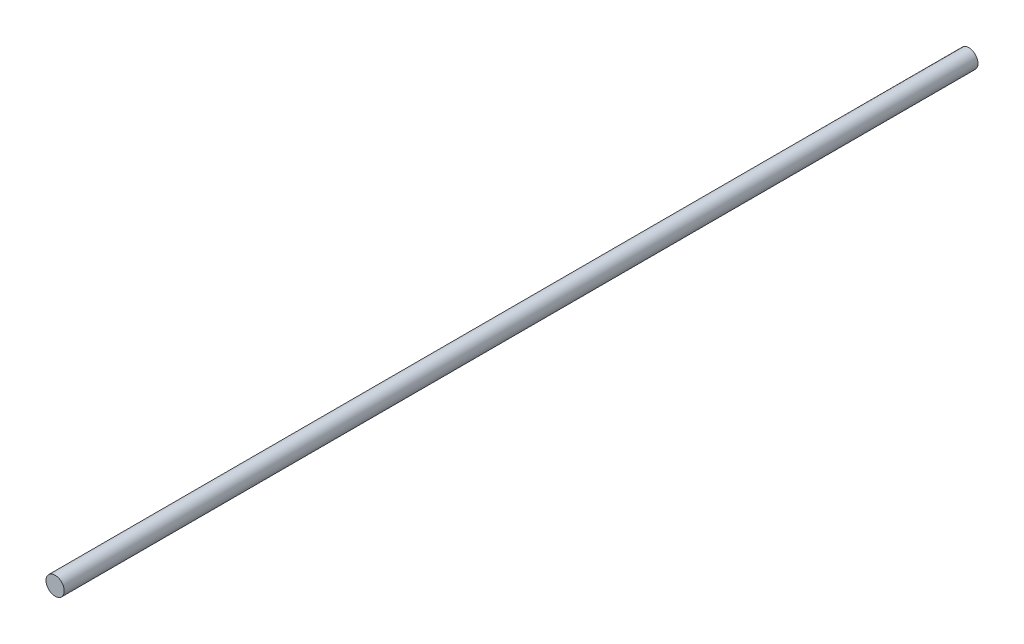
SolidWorks part; units mm, degrees
ref_plane "Plan de face" through (0, 0, 0) normal (0, 0, 1) x (1, 0, 0)
ref_plane "Plan de dessus" through (0, 0, 0) normal (0, 1, 0) x (1, 0, 0)
ref_plane "Plan de droite" through (0, 0, 0) normal (1, 0, 0) x (0, 0, -1)
sketch "Esquisse1" plane through (0, 0, 0) normal (0, 0, 1) x (1, 0, 0)
  circle A0 centre (0, 0) radius 5
  dimension "D1" = 10
extrude "Boss.-Extru.1" add sketch "Esquisse1" along normal blind 500
